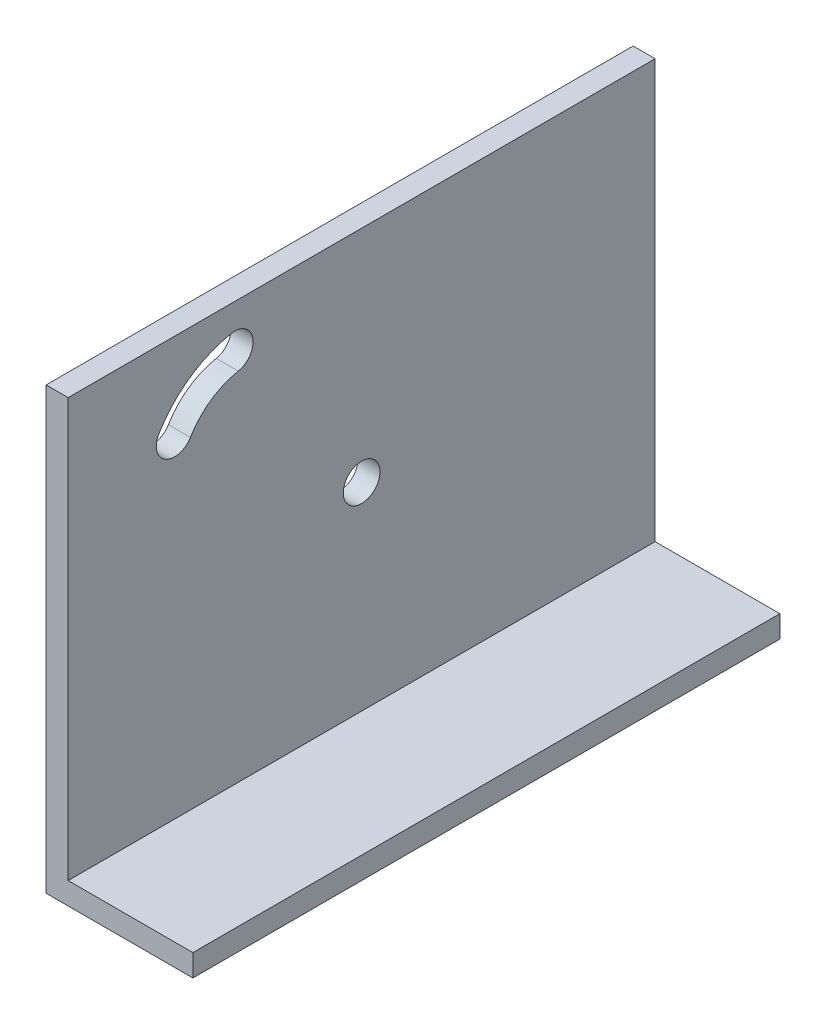
SolidWorks part; units mm, degrees
ref_plane "Front Plane" through (0, 0, 0) normal (0, 0, 1) x (1, 0, 0)
ref_plane "Top Plane" through (0, 0, 0) normal (0, 1, 0) x (1, 0, 0)
ref_plane "Right Plane" through (0, 0, 0) normal (1, 0, 0) x (0, 0, -1)
sketch "Sketch1" plane through (0, 0, 0) normal (0, 0, 1) x (1, 0, 0)
  line L1 (0, 0) -> (20, 0)
  line L2 (0, 0) -> (0, 60)
  line L3 (0, 60) -> (3, 60)
  line L4 (20, 0) -> (20, 3)
  line L7 (20, 3) -> (3, 3)
  line L8 (3, 60) -> (3, 3)
  dimension "D1" = 60
  dimension "D2" = 20
  dimension "D3" = 3
  dimension "D4" = 3
extrude "Boss-Extrude1" add sketch "Sketch1" along normal blind 80
sketch "Sketch2" plane through (0, 0, 0) normal (-1, 0, 0) x (0, 0, 1)
  line L0 (80, 0) -> (0, 0) construction
  circle A0 centre (40, 30) radius 2.5
  point P6 (40, 0)
  dimension "D2" = 5
  dimension "D1" = 30
extrude "Cut-Extrude1" cut sketch "Sketch2" against normal through all
sketch "Sketch3" plane through (0, 0, 0) normal (-1, 0, 0) x (0, 0, 1)
  line L0 (40, 60) -> (40, 45.6586) construction
  line L1 (0, 60) -> (18, 60) construction
  line L2 (0, 60) -> (0, 52) construction
  line L3 (0, 52) -> (18, 52) construction
  line L4 (18, 60) -> (18, 52) construction
  line L5 (0, 60) -> (25, 60) construction
  line L6 (0, 60) -> (0, 42) construction
  line L7 (0, 42) -> (25, 42) construction
  line L8 (25, 60) -> (25, 42) construction
  line L9 (80, 60) -> (0, 60) construction
  arc A0 (14.518, 48.2553) -> (22.7104, 53.9899) centre (25, 42) cw construction
  arc A1 (22.2414, 56.4455) -> (12.3712, 49.5364) centre (25, 42) ccw construction
  arc A2 (23.1793, 51.5343) -> (16.6648, 46.9741) centre (25, 42) ccw construction
  arc A3 (23.1793, 51.5343) -> (22.2414, 56.4455) centre (22.7104, 53.9899) ccw construction
  arc A4 (12.3712, 49.5364) -> (16.6648, 46.9741) centre (14.518, 48.2553) ccw construction
  arc A5 (65.482, 48.2553) -> (57.2896, 53.9899) centre (55, 42) ccw construction
  arc A6 (57.7586, 56.4455) -> (67.6288, 49.5364) centre (55, 42) cw
  arc A7 (56.8207, 51.5343) -> (63.3352, 46.9741) centre (55, 42) cw
  arc A8 (56.8207, 51.5343) -> (57.7586, 56.4455) centre (57.2896, 53.9899) cw
  arc A9 (67.6288, 49.5364) -> (63.3352, 46.9741) centre (65.482, 48.2553) cw
  point P3 (18, 52)
  point P23 (62, 52)
  dimension "D1" = 2.5
  dimension "D2" = 8
  dimension "D3" = 18
  dimension "D4" = 10
  dimension "D5" = 18
  dimension "D6" = 25
extrude "Cut-Extrude2" cut sketch "Sketch3" against normal blind 10
